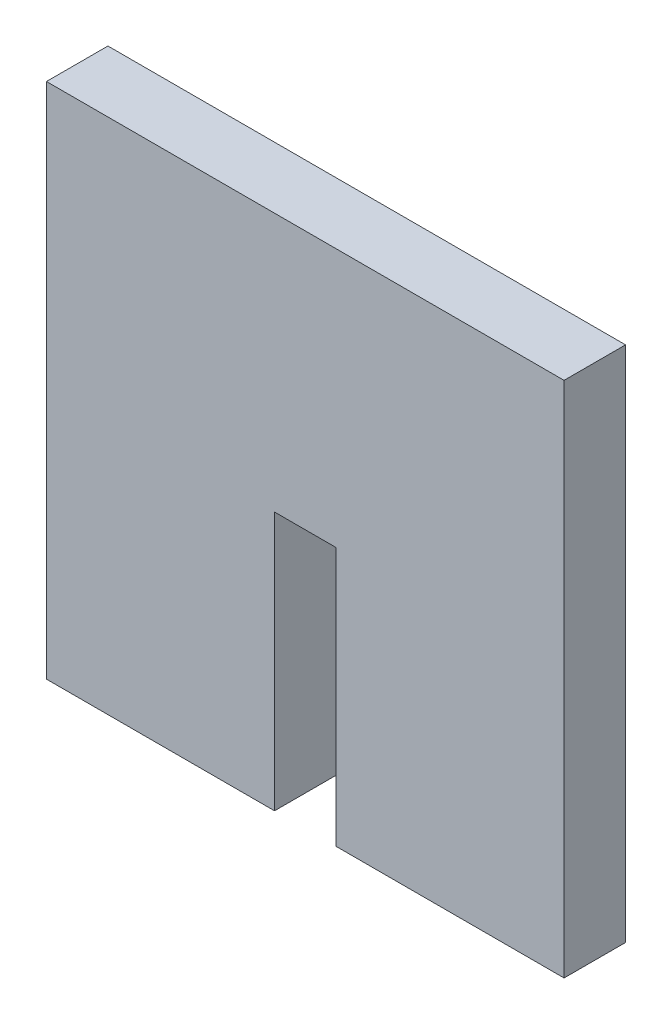
SolidWorks part; units mm, degrees
material "Balsa"
ref_plane "Front Plane" through (0, 0, 0) normal (0, 0, 1) x (1, 0, 0)
ref_plane "Top Plane" through (0, 0, 0) normal (0, 1, 0) x (1, 0, 0)
ref_plane "Right Plane" through (0, 0, 0) normal (1, 0, 0) x (0, 0, -1)
sketch "Sketch1" plane through (0, 0, 0) normal (0, 0, 1) x (1, 0, 0)
  line L0 (16.021, 9.09) -> (0, 9.09) construction
  line L1 (0, 0) -> (16.021, 0)
  line L2 (0, 0) -> (0, 36.36)
  line L3 (0, 36.36) -> (36.36, 36.36)
  line L4 (36.36, 0) -> (36.36, 36.36)
  line L6 (16.021, 0) -> (16.021, 18.18)
  line L7 (16.021, 18.18) -> (20.339, 18.18)
  line L8 (20.339, 0) -> (20.339, 18.18)
  line L9 (20.339, 9.09) -> (36.36, 9.09) construction
  line L10 (20.339, 0) -> (36.36, 0)
  dimension "D1" = 36.36
  dimension "D2" = 36.36
  dimension "D3" = 18.18
  dimension "D4" = 4.318
extrude "Boss-Extrude1" add sketch "Sketch1" along normal blind 4.318
